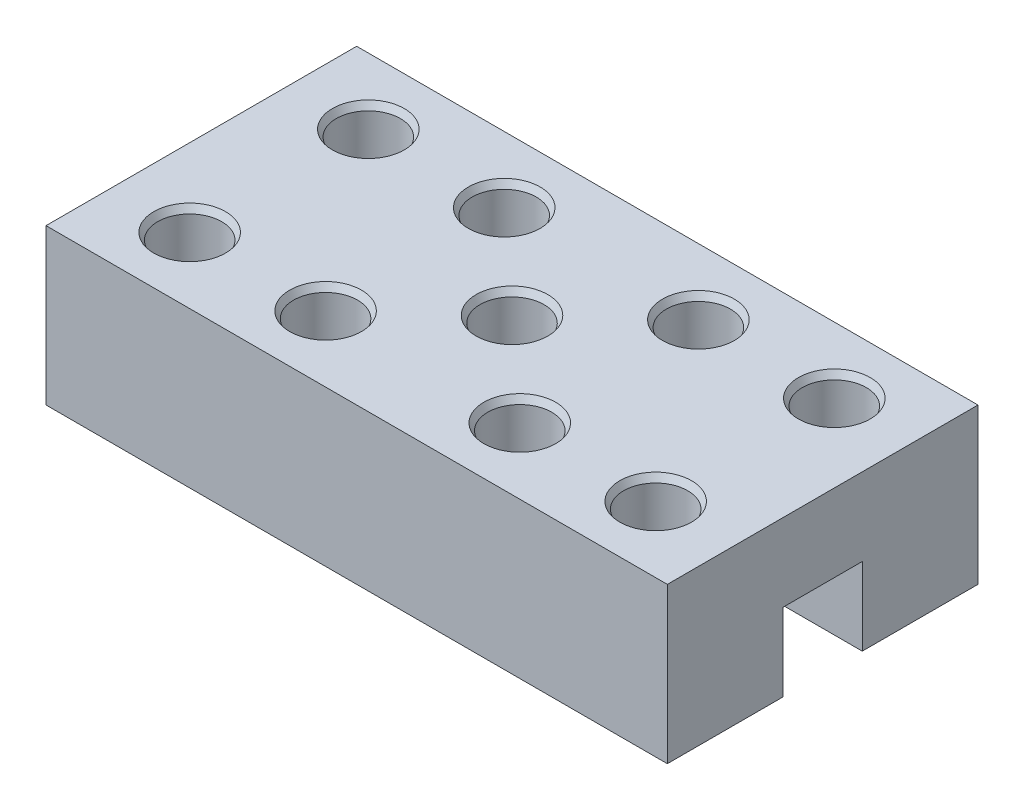
SolidWorks part; units mm, degrees
ref_plane "Спереди" through (0, 0, 0) normal (0, 0, 1) x (1, 0, 0)
ref_plane "Сверху" through (0, 0, 0) normal (0, 1, 0) x (1, 0, 0)
ref_plane "Справа" through (0, 0, 0) normal (1, 0, 0) x (0, 0, -1)
sketch "Sketch1" plane through (0, 0, 0) normal (0, 1, 0) x (1, 0, 0)
  line L1 (40, -20) -> (-40, -20)
  line L2 (40, -20) -> (40, 20)
  line L3 (40, 20) -> (-40, 20)
  line L4 (-40, -20) -> (-40, 20)
  line L5 (40, -20) -> (-40, 20) construction
  line L6 (40, 20) -> (-40, -20) construction
  point P0 (0, 0)
  dimension "D1" = 80
  dimension "D2" = 40
extrude "Boss-Extrude1" add sketch "Sketch1" along normal blind 20
sketch "Sketch2" plane through (-40, 0, 0) normal (-1, 0, 0) x (0, 0, 1)
  line L0 (0, 20) -> (0, 0) construction
  line L1 (-20, 20) -> (20, 20) construction
  line L2 (-20, 0) -> (20, 0) construction
  line L4 (5.1, -10) -> (-5.1, -10)
  line L5 (5.1, -10) -> (5.1, 10)
  line L6 (5.1, 10) -> (-5.1, 10)
  line L7 (-5.1, -10) -> (-5.1, 10)
  line L8 (5.1, -10) -> (-5.1, 10) construction
  line L9 (5.1, 10) -> (-5.1, -10) construction
  dimension "D1" = 10.2
  dimension "D2" = 20
extrude "Cut-Extrude1" cut sketch "Sketch2" against normal through all
sketch "Sketch3" plane through (0, 20, 0) normal (0, 1, 0) x (1, 0, 0)
  line L0 (0, -20) -> (0, 20) construction
  line L1 (-40, -20) -> (40, -20) construction
  line L2 (40, 20) -> (-40, 20) construction
  line L4 (-12.5, 11.5) -> (12.5, 11.5) construction
  line L5 (-12.5, 11.5) -> (-12.5, -11.5) construction
  line L6 (-12.5, -11.5) -> (12.5, -11.5) construction
  line L7 (12.5, 11.5) -> (12.5, -11.5) construction
  line L8 (-12.5, 11.5) -> (12.5, -11.5) construction
  line L9 (-12.5, -11.5) -> (12.5, 11.5) construction
  line L10 (-30, 11.5) -> (30, 11.5) construction
  line L11 (-30, 11.5) -> (-30, -11.5) construction
  line L12 (-30, -11.5) -> (30, -11.5) construction
  line L13 (30, 11.5) -> (30, -11.5) construction
  line L14 (-30, 11.5) -> (30, -11.5) construction
  line L15 (-30, -11.5) -> (30, 11.5) construction
  circle A0 centre (12.5, -11.5) radius 4.125
  circle A1 centre (-12.5, -11.5) radius 4.125
  circle A2 centre (-12.5, 11.5) radius 4.125
  circle A3 centre (12.5, 11.5) radius 4.125
  circle A4 centre (30, -11.5) radius 4.125
  circle A5 centre (-30, -11.5) radius 4.125
  circle A6 centre (-30, 11.5) radius 4.125
  circle A7 centre (30, 11.5) radius 4.125
  circle A8 centre (0, 0) radius 4.125
  point P6 (0, 0)
  point P15 (0, 0)
  dimension "D1" = 8.25
  dimension "D2" = 25
  dimension "D3" = 23
  dimension "D4" = 60
extrude "Cut-Extrude2" cut sketch "Sketch3" against normal through all
chamfer "Chamfer1" distance 0.5 angle 60 9 edges at (30, 20, -7.375) (12.5, 20, -7.375) (0, 20, 4.125) (-12.5, 20, -7.375) (-30, 20, -7.375) (-30, 20, 15.625) (-12.5, 20, 15.625) (12.5, 20, 15.625) (30, 20, 15.625)
